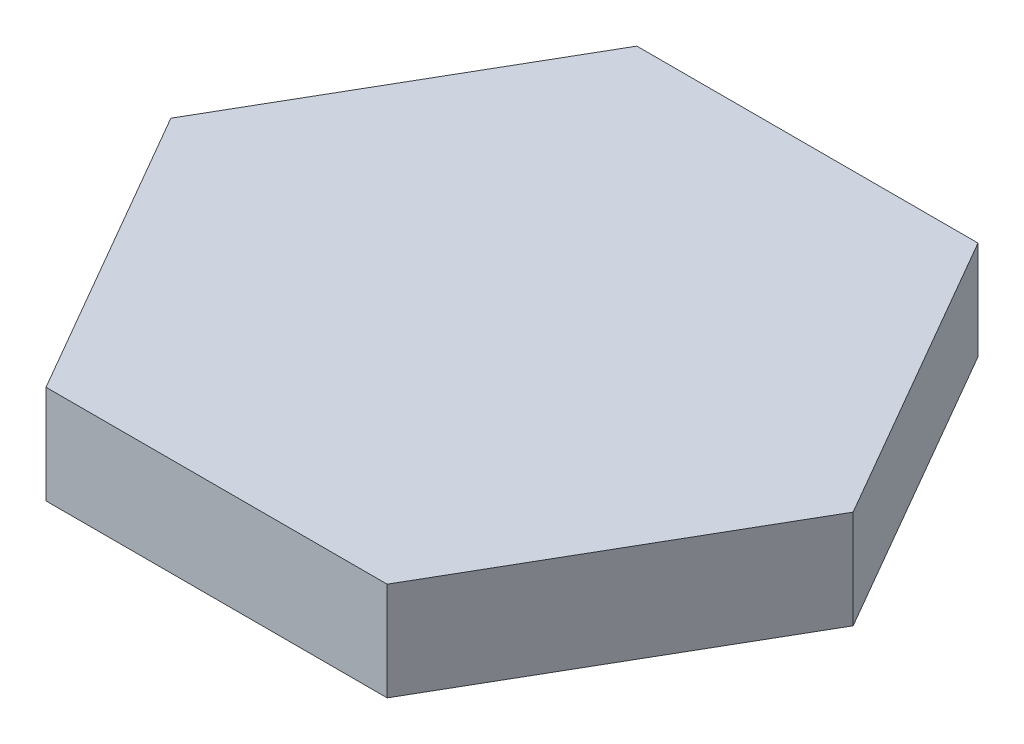
SolidWorks part; units mm, degrees
ref_plane "Front Plane" through (0, 0, 0) normal (0, 0, 1) x (1, 0, 0)
ref_plane "Top Plane" through (0, 0, 0) normal (0, 1, 0) x (1, 0, 0)
ref_plane "Right Plane" through (0, 0, 0) normal (1, 0, 0) x (0, 0, -1)
sketch "Sketch1" plane through (0, 0, 0) normal (0, 1, 0) x (1, 0, 0)
  line L1 (5.1962, 9) -> (-5.1962, 9)
  line L2 (-5.1962, 9) -> (-10.3923, 0)
  line L3 (-10.3923, 0) -> (-5.1962, -9)
  line L4 (-5.1962, -9) -> (5.1962, -9)
  line L5 (5.1962, -9) -> (10.3923, 0)
  line L6 (10.3923, 0) -> (5.1962, 9)
  circle A0 centre (0, 0) radius 9 construction
  dimension "D1" = 18
extrude "Boss-Extrude1" add sketch "Sketch1" along normal blind 3
